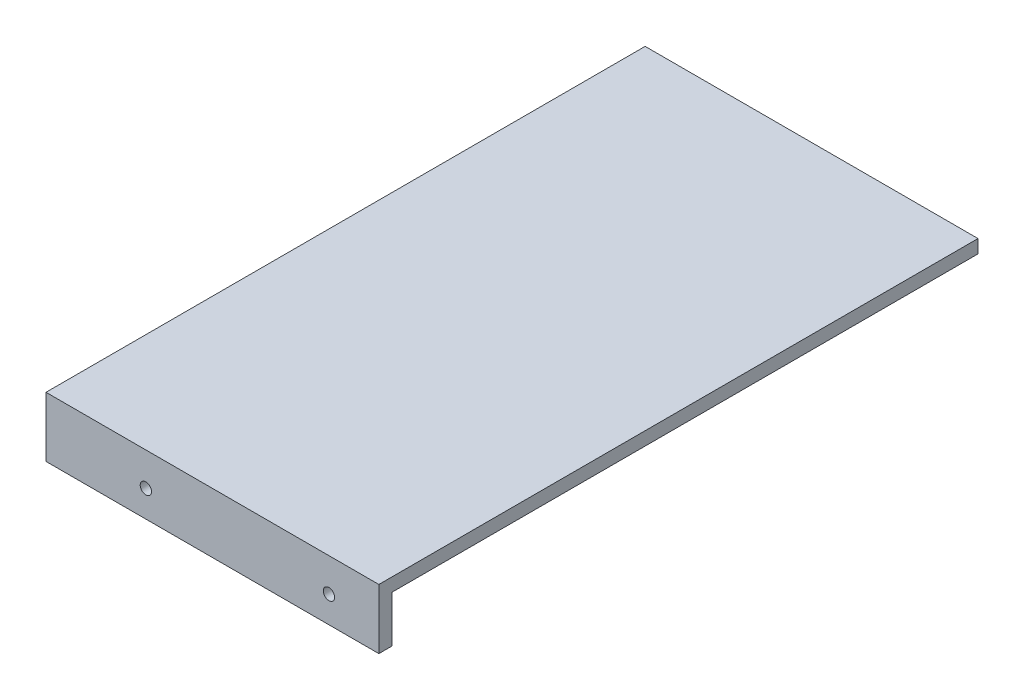
SolidWorks part; units mm, degrees
ref_plane "Front Plane" through (0, 0, 0) normal (0, 0, 1) x (1, 0, 0)
ref_plane "Top Plane" through (0, 0, 0) normal (0, 1, 0) x (1, 0, 0)
ref_plane "Right Plane" through (0, 0, 0) normal (1, 0, 0) x (0, 0, -1)
sketch "Sketch1" plane through (-1647.1695, 0, 0) normal (1, 0, 0) x (0, 0, -1)
  line L0 (-1369.8257, 767.8493) -> (-1369.8257, 763.1367) construction
  line L1 (-1369.8257, 769.8493) -> (-1189.8257, 769.8493)
  line L2 (-1369.8257, 769.8493) -> (-1369.8257, 751.8493)
  line L3 (-1369.8257, 751.8493) -> (-1189.8257, 751.8493)
  line L4 (-1189.8257, 769.8493) -> (-1189.8257, 751.8493)
  line L5 (-1369.8257, 769.8493) -> (-789.8257, 769.8493) construction
  line L6 (-1369.8257, 751.8493) -> (-789.8257, 751.8493) construction
  line L7 (-1339.8257, 756.5619) -> (-1339.8257, 763.1367) construction
  line L8 (-1369.8257, 756.5619) -> (-789.8257, 756.5619) construction
  line L9 (-1369.8257, 763.1367) -> (-789.8257, 763.1367) construction
  line L10 (-1339.8257, 759.8493) -> (-1219.8257, 759.8493) construction
  circle A0 centre (-1219.8257, 759.8493) radius 1.7
  circle A1 centre (-1339.8257, 759.8493) radius 1.7
  dimension "D4" = 3.4
  dimension "D5" = 3.4
  dimension "D1" = 180
  dimension "D2" = 30
  dimension "D3" = 30
extrude "Boss-Extrude1" add sketch "Sketch1" along normal blind 4
sketch "Sketch2" plane through (0, 0, 1369.8257) normal (0, 0, -1) x (-1, 0, 0)
  line L0 (1647.1695, 751.8493) -> (967.1695, 751.8493) construction
  line L1 (1647.1695, 769.8493) -> (1547.1695, 769.8493)
  line L2 (1647.1695, 769.8493) -> (1647.1695, 751.8493)
  line L3 (1647.1695, 751.8493) -> (1547.1695, 751.8493)
  line L4 (1547.1695, 769.8493) -> (1547.1695, 751.8493)
  line L5 (1617.1695, 763.1367) -> (1617.1695, 756.5619) construction
  line L6 (1647.1695, 763.1367) -> (967.1695, 763.1367) construction
  line L7 (1647.1695, 756.5619) -> (967.1695, 756.5619) construction
  line L8 (1617.1695, 759.8493) -> (1562.1695, 759.8493) construction
  circle A0 centre (1617.1695, 759.8493) radius 1.7
  circle A1 centre (1562.1695, 759.8493) radius 1.7
  dimension "D4" = 3.4
  dimension "D5" = 3.4
  dimension "D1" = 100
  dimension "D2" = 30
  dimension "D3" = 15
extrude "Boss-Extrude2" add sketch "Sketch2" along normal blind 4
sketch "Sketch3" plane through (0, 0, 1365.8257) normal (0, 0, -1) x (-1, 0, 0)
  line L0 (1643.1695, 751.8493) -> (1643.1695, 769.8493) construction
  line L1 (1547.1695, 769.8493) -> (1643.1695, 769.8493)
  line L2 (1547.1695, 769.8493) -> (1547.1695, 765.8493)
  line L3 (1547.1695, 765.8493) -> (1643.1695, 765.8493)
  line L4 (1643.1695, 769.8493) -> (1643.1695, 765.8493)
  dimension "D1" = 4
extrude "Boss-Extrude3" add sketch "Sketch3" along normal up to surface (176 mm away) up to face at (-1645.1695, 760.8493, 1189.8257)
